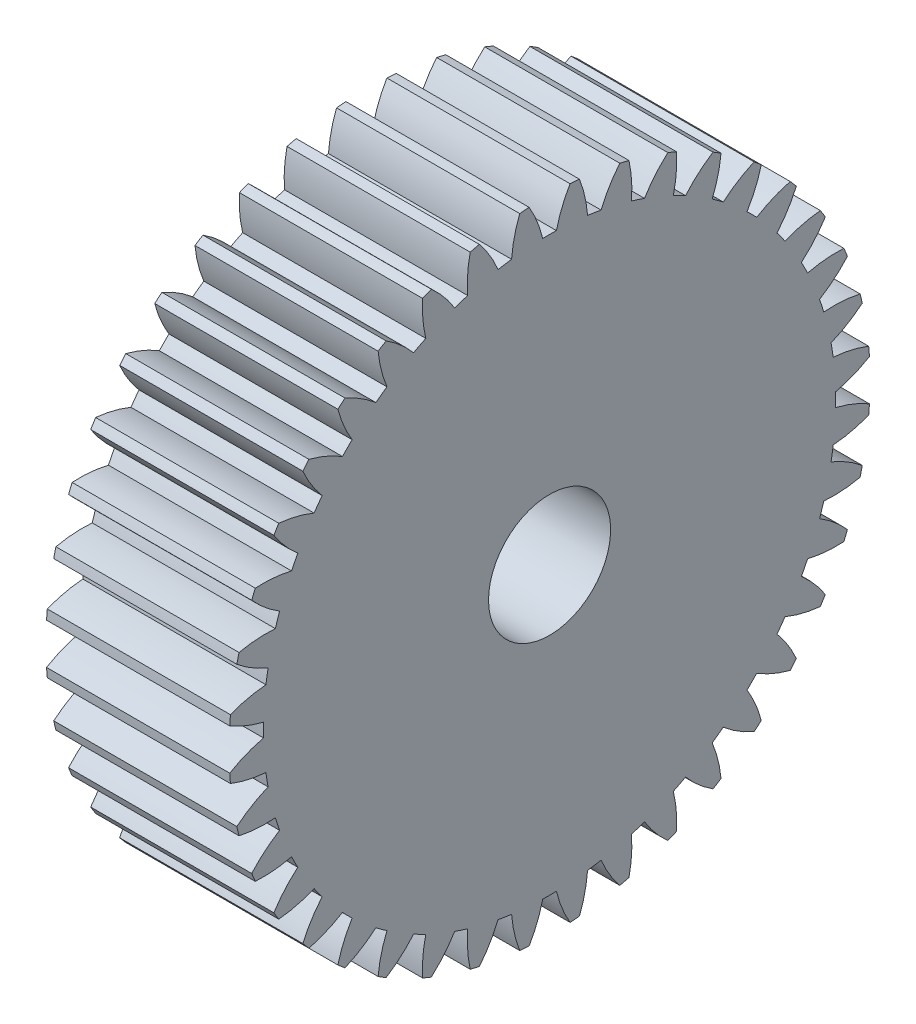
SolidWorks part; units mm, degrees
ref_plane "Plane1" through (0, 0, 0) normal (0, 0, 1) x (1, 0, 0)
ref_plane "Plane2" through (0, 0, 0) normal (0, 1, 0) x (1, 0, 0)
ref_plane "Plane3" through (0, 0, 0) normal (1, 0, 0) x (0, 0, -1)
sketch "HoldingSke" plane through (0, 0, 0) normal (0, 1, 0) x (1, 0, 0)
  line L0 (0, 0) -> (0.766, -0.6428)
  line L1 (-15, 0) -> (100, 0) construction
  line L2 (0, 0) -> (-2.1039, 2.3779)
  line L3 (0, 0) -> (-11.863, 4.5341)
  line L4 (0, 0) -> (6.6156, 5.5511)
  line L5 (0, 0) -> (-46.8476, -17.4728)
  line L6 (0, 0) -> (-9.9476, -6.7116)
  line L7 (-2.1039, 2.3779) -> (8.6586, 51.2059)
  line L8 (-76.2, 54.61) -> (-74.8, 54.61)
  line L9 (-71.009, 38.7566) -> (-53.1078, 45.2721)
  line L10 (-76.2, 71.12) -> (104.1128, 71.12)
  line L11 (0, 0) -> (-12, 0)
  line L12 (-76.2, 101.6) -> (-76.162, 101.6)
  line L13 (24.9733, 27.94) -> (52.9518, 28.4284)
  line L14 (24.9733, 27.94) -> (24.9743, 27.94)
  line L15 (24.9733, 27.94) -> (100.4006, 29.5858)
  line L16 (-63.627, -1) -> (-12.827, -1)
  circle A0 centre (0, 0) radius 4
  circle A1 centre (0, 0) radius 18.749
  circle A2 centre (0, 0) radius 37.5
  circle A3 centre (0, 0) radius 4
  dimension "MHD" = 37.498
  dimension "Hub_dia" = 75
  dimension "Bore" = 8
  dimension "MBD" = 8
  dimension "Num_teeth" = 40
  dimension "Pitch" = 1
  dimension "Overall_len" = 50
  dimension "Show_teeth" = 40
  dimension "Thickness" = 12
  dimension "OAL" = 50.0001
  dimension "T_dim" = 1.4
  dimension "Ap" = 20
  dimension "H" = 19.05
  dimension "Pitch_radius" = 180.3128
  dimension "Width" = 12
  dimension "Backlash" = 0.038
  dimension "Addendum_fac" = 1
  dimension "Dedendum_fac" = 1.25
  dimension "Clearance_fac" = 0.25
  dimension "Dedendum_add" = 0.001
  dimension "Module" = 1
sketch "BasProSke" plane through (0, 0, 0) normal (0, 1, 0) x (1, 0, 0)
  line L0 (-10, 0) -> (60, 0) construction
  line L1 (0, 0) -> (0, 21)
  line L2 (0, 0) -> (12, 0)
  line L3 (12, 0) -> (12, 21)
  line L4 (12, 21) -> (0, 21)
  dimension "Thickness" = 12
  dimension "Diameter" = 42
revolve "Base-Revolve" add sketch "BasProSke" angle 360 about L0
sketch "TooCutSke" plane through (0, 0, 0) normal (1, 0, 0) x (0, 0, -1)
  line L1 (0, 0) -> (0, 107) construction
  line L2 (0, 0) -> (-0.8517, 19.9819) construction
  line L3 (0, 0) -> (-3.1363, 39.8509) construction
  line L4 (-0.8517, 19.9819) -> (-1.5682, 19.9255) construction
  arc A0 (0.4487, 18.7436) -> (-0.4487, 18.7436) centre (0, 0) ccw
  arc A1 (1.3547, 20.9817) -> (-1.3547, 20.9817) centre (0, 0) ccw
  circle A2 centre (0, 0) radius 20 construction
  circle A3 centre (0, 0) radius 18.7939 construction
  arc A4 (-0.4487, 18.7436) -> (-1.3547, 20.9817) centre (-8.2322, 16.895) ccw
  arc A5 (1.3547, 20.9817) -> (0.4487, 18.7436) centre (8.2322, 16.895) ccw
  dimension "Root_dia" = 37.498
  dimension "Overcut_dia" = 42.0508
  dimension "Pitch_dia" = 40
  dimension "Base_dia" = 37.5877
  dimension "Flank_rad" = 8
  dimension "Half_ang" = 4.5
  dimension "Half_CT" = 0.7187
extrude "ToothCut" cut sketch "TooCutSke" along normal through all
fillet "Breaks" [suppressed] radius 0.02
fillet "RootFillets" [suppressed] radius 0.251
pattern_circular "TeethCuts" count 40 every 9 about axis through (-10, 0, 0) along (1, 0, 0) of "ToothCut", "RootFillets", "Breaks"
sketch "HubNeaOneSke" plane through (0, 0, 0) normal (-1, 0, 0) x (0, 0, 1)
  circle A0 centre (0, 0) radius 18.749
  dimension "Diameter" = 37.498
extrude "HubNearOne" [suppressed] add sketch "HubNeaOneSke" along normal blind 38.0001
sketch "HubNeaBotSke" plane through (0, 0, 0) normal (-1, 0, 0) x (0, 0, 1)
  circle A0 centre (0, 0) radius 18.749
  dimension "Diameter" = 37.498
extrude "HubNearBoth" [suppressed] add sketch "HubNeaBotSke" along normal blind 19
ref_plane "FarPln" through (12, 0, 0) normal (1, 0, 0) x (0, 0, -1)
sketch "HubFarSke" plane through (12, 0, 0) normal (1, 0, 0) x (0, 0, -1)
  circle A0 centre (0, 0) radius 18.749
  dimension "Diameter" = 37.498
extrude "HubFar" [suppressed] add sketch "HubFarSke" along normal blind 19
sketch "BorSke" plane through (0, 0, 0) normal (1, 0, 0) x (0, 0, -1)
  circle A0 centre (0, 0) radius 4
  dimension "Diameter" = 8
extrude "Bore" cut sketch "BorSke" along normal mid plane 100.0001
sketch "KeySke" plane through (0, 0, 0) normal (1, 0, 0) x (0, 0, -1)
  line L0 (-1.5, 0) -> (-1.5, 5.4)
  line L1 (-1.5, 5.4) -> (1.5, 5.4)
  line L2 (1.5, 5.4) -> (1.5, 0)
  line L3 (0, 0) -> (0, 34) construction
  line L4 (-1.5, 0) -> (1.5, 0)
  dimension "Offset" = 5.4
  dimension "Width" = 3
extrude "Keyway" [suppressed] cut sketch "KeySke" along normal mid plane 100.0001
pattern_circular "Keyway2" [suppressed] count 2 every 90 about axis through (-10, 0, 0) along (1, 0, 0)
equation "' \"Module@HoldingSke\" = 6.35"
equation "' \"Num_teeth@HoldingSke\" = 12"
equation "' \"Ap@HoldingSke\" =  20"
equation "' \"Ap@HoldingSke\" = 20"
equation "' \"Width@HoldingSke\" = 0.5 * 25.4"
equation "' \"Hub_dia@HoldingSke\"= 1 * 25.4"
equation "' \"Hub_dia@HoldingSke\" = 1 * 25.4"
equation "' \"Overall_len@HoldingSke\" = 1.0 * 25.4"
equation "' \"Bore@HoldingSke\" = 0.75 * 25.4"
equation "' \"T_dim@HoldingSke\" = 0.1 * 25.4"
equation "' \"Width@KeySke\" = 0.25 * 25.4"
equation "' \"Show_teeth@HoldingSke\" = 13"
equation "' \"Backlash@HoldingSke\" = 0.009 * 25.4"
equation "' \"Addendum_fac@HoldingSke\" = 1.0"
equation "' \"Dedendum_fac@HoldingSke\" = 1.25"
equation "' \"Dedendum_add@HoldingSke\" = 0.00005 * 25.4"
equation "' \"Clearance_fac@HoldingSke\" = 0.25"
equation "\"Pitch@HoldingSke\" = 1 / \"Module@HoldingSke\""
equation "\"Overcut_dia@TooCutSke\" = (\"Num_teeth@HoldingSke\" + 2 * \"Addendum_fac@HoldingSke\") / \"Pitch@HoldingSke\" + 0.002 * 25.4"
equation "\"Pitch_dia@TooCutSke\" = \"Num_teeth@HoldingSke\" / \"Pitch@HoldingSke\""
equation "\"Base_dia@TooCutSke\" = \"Num_teeth@HoldingSke\" / \"Pitch@HoldingSke\" * cos((\"Ap@HoldingSke\"  * 3.14159265 / 180))"
equation "\"Root_dia@TooCutSke\" = (\"Num_teeth@HoldingSke\" + 2) / \"Pitch@HoldingSke\" - 2 * (\"Addendum_fac@HoldingSke\" + \"Dedendum_fac@HoldingSke\") / \"Pitch@HoldingSke\" - \"Dedendum_add@HoldingSke\" * 2"
equation "\"Half_ang@TooCutSke\" = 180 / \"Num_teeth@HoldingSke\""
equation "\"Half_CT@TooCutSke\" = \"Num_teeth@HoldingSke\" / \"Pitch@HoldingSke\" * sin((3.14159265 / 2 / \"Num_teeth@HoldingSke\")) / 2 - 7 * \"Backlash@HoldingSke\" / 4"
equation "\"Flank_rad@TooCutSke\" = \"Num_teeth@HoldingSke\" / \"Pitch@HoldingSke\" / 5"
equation "\"Radius@RootFillets\" = \"Clearance_fac@HoldingSke\" / \"Pitch@HoldingSke\" + \"Dedendum_add@HoldingSke\""
equation "\"Break_rad@Breaks\" = 0.02 / \"Pitch@HoldingSke\""
equation "\"Thickness@HoldingSke\" = \"Width@HoldingSke\""
equation "\"OAL@HoldingSke\" = \"Thickness@HoldingSke\""
equation "\"MHD@HoldingSke\" = (\"Num_teeth@HoldingSke\" + 2) / \"Pitch@HoldingSke\" - 2 * (\"Addendum_fac@HoldingSke\" + \"Dedendum_fac@HoldingSke\")  / \"Pitch@HoldingSke\" - \"Dedendum_add@HoldingSke\" * 2"
equation "\"MBD@HoldingSke\" = (\"Num_teeth@HoldingSke\" + 2) / \"Pitch@HoldingSke\" - 2 * (\"Addendum_fac@HoldingSke\" + \"Dedendum_fac@HoldingSke\")  / \"Pitch@HoldingSke\" - \"Dedendum_add@HoldingSke\" * 2 - 0.002 * 25.4"
equation "\"MHD@HoldingSke\" = ((sgn( \"MHD@HoldingSke\" - \"Hub_dia@HoldingSke\" )-1)*( \"MHD@HoldingSke\" - \"Hub_dia@HoldingSke\" ))/-2+ \"Hub_dia@HoldingSke\""
equation "\"MBD@HoldingSke\" = ((sgn( \"MBD@HoldingSke\" - \"Bore@HoldingSke\" )-1)*( \"MBD@HoldingSke\" - \"Bore@HoldingSke\" ))/-2+ \"Bore@HoldingSke\""
equation "\"OAL@HoldingSke\" = ((sgn( \"OAL@HoldingSke\" - \"Overall_len@HoldingSke\" )+1)*( \"OAL@HoldingSke\" - \"Overall_len@HoldingSke\" ))/2 + \"Overall_len@HoldingSke\" + 0.000002 * 25.4"
equation "\"Num_teeth@TeethCuts\" = int( \"Show_teeth@HoldingSke\" ) + 1"
equation "\"Num_teeth@TeethCuts\" = ((sgn( \"Num_teeth@TeethCuts\" - \"Num_teeth@HoldingSke\" )-1)*( \"Num_teeth@TeethCuts\" - \"Num_teeth@HoldingSke\" ))/-2+ \"Num_teeth@HoldingSke\""
equation "\"Num_teeth@TeethCuts\" = ((sgn( \"Num_teeth@TeethCuts\" - 2.0)+1)*( \"Num_teeth@TeethCuts\" - 2.0))/2 +2.0"
equation "\"Angle@TeethCuts\" = 360.0 / \"Num_teeth@HoldingSke\""
equation "\"Diameter@BasProSke\" = (\"Num_teeth@HoldingSke\" + 2 * \"Addendum_fac@HoldingSke\") / \"Pitch@HoldingSke\""
equation "\"Thickness@BasProSke\"  = \"Thickness@HoldingSke\""
equation "' \"Fillet_rad@BasProSke\" =  \"Thickness@HoldingSke\" * 0.05"
equation "' \"Fillet_rad@BasProSke\" = \"Thickness@HoldingSke\" * 0.05"
equation "\"MHD@HoldingSke\" = ((sgn( \"MHD@HoldingSke\" - \"Root_dia@TooCutSke\" )-1)*( \"MHD@HoldingSke\" - \"Root_dia@TooCutSke\" ))/-2+ \"Root_dia@TooCutSke\""
equation "\"Diameter@HubNeaOneSke\" = \"MHD@HoldingSke\""
equation "\"Length@HubNearOne\" = \"OAL@HoldingSke\" - \"Thickness@BasProSke\""
equation "\"Diameter@HubNeaBotSke\" = \"MHD@HoldingSke\""
equation "\"Length@HubNearBoth\" = ( \"OAL@HoldingSke\" - \"Thickness@BasProSke\" ) / 2.0"
equation "\"Thickness@FarPln\" = \"Thickness@BasProSke\""
equation "\"Diameter@HubFarSke\" = \"MHD@HoldingSke\""
equation "\"Length@HubFar\" = ( \"OAL@HoldingSke\" - \"Thickness@BasProSke\" ) / 2.0"
equation "\"Diameter@BorSke\" = \"MBD@HoldingSke\""
equation "\"D1@Bore\" = \"OAL@HoldingSke\" * 2.0"
equation "\"D1@Keyway\" = \"OAL@HoldingSke\" * 2.0"
equation "\"Offset@KeySke\" = \"T_dim@HoldingSke\" + \"MBD@HoldingSke\" / 2.0"
